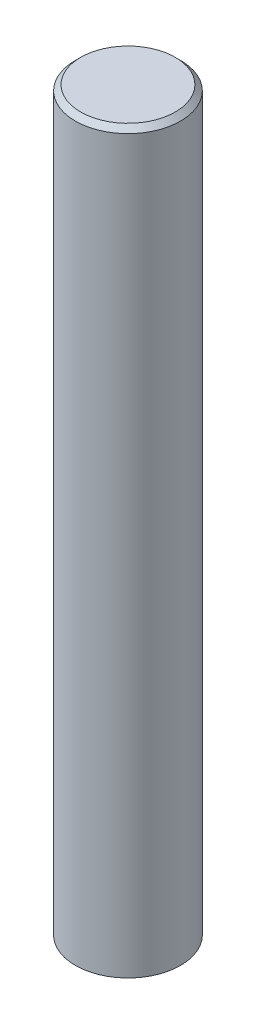
SolidWorks part; units mm, degrees
ref_plane "Front Plane" through (0, 0, 0) normal (0, 0, 1) x (1, 0, 0)
ref_plane "Top Plane" through (0, 0, 0) normal (0, 1, 0) x (1, 0, 0)
ref_plane "Right Plane" through (0, 0, 0) normal (1, 0, 0) x (0, 0, -1)
sketch "Sketch1" plane through (0, 0, 0) normal (0, 1, 0) x (1, 0, 0)
  circle A0 centre (0, 0) radius 10
  dimension "D1" = 20
extrude "Boss-Extrude1" add sketch "Sketch1" along normal blind 140
chamfer "Chamfer1" distance 1 angle 45 1 edges at (0, 140, 10)
